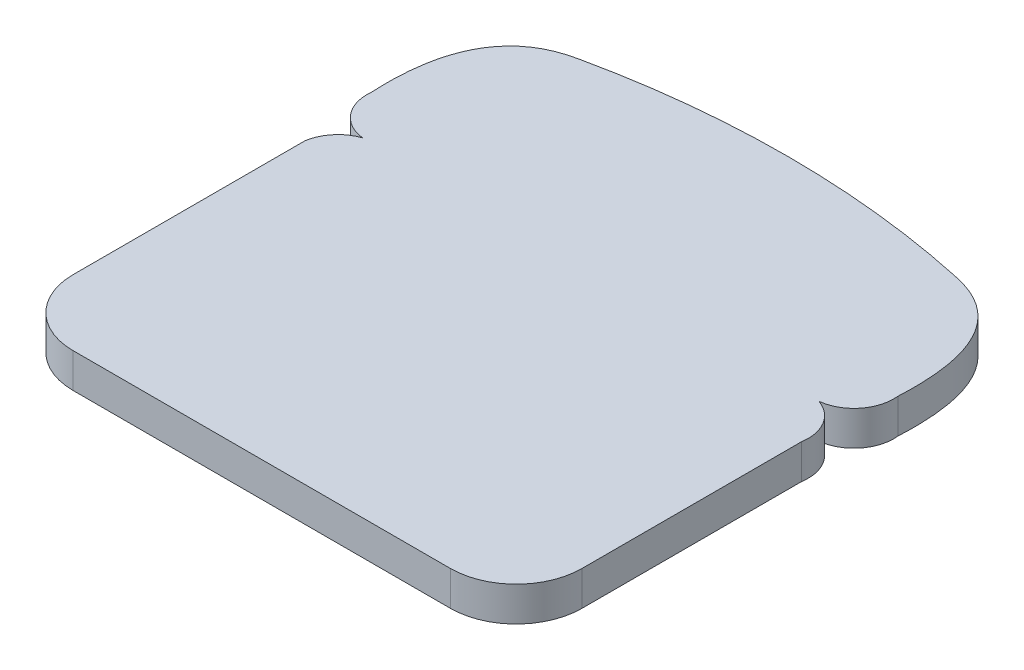
SolidWorks part; units mm, degrees
material "Teak"
ref_plane "Front Plane" through (0, 0, 0) normal (0, 0, 1) x (1, 0, 0)
ref_plane "Top Plane" through (0, 0, 0) normal (0, 1, 0) x (1, 0, 0)
ref_plane "Right Plane" through (0, 0, 0) normal (1, 0, 0) x (0, 0, -1)
sketch "Sketch2" plane through (0, 0, 0) normal (0, 1, 0) x (1, 0, 0)
  line L0 (-66.04, 22.225) -> (66.04, 22.225)
  line L1 (63.5, -66.675) -> (-63.5, -66.675)
  line L2 (63.5, -66.675) -> (63.5, 66.675)
  line L3 (63.5, 66.675) -> (-63.5, 66.675)
  line L4 (-63.5, -66.675) -> (-63.5, 66.675)
  line L5 (63.5, -66.675) -> (-63.5, 66.675) construction
  line L6 (63.5, 66.675) -> (-63.5, -66.675) construction
  line L7 (-73.66, 9.525) -> (-73.66, -53.975)
  line L8 (-54.61, -73.025) -> (54.61, -73.025)
  line L9 (73.66, -53.975) -> (73.66, 9.525)
  line L10 (-73.66, 9.525) -> (-73.66, 13.1711)
  line L11 (0, 79.1198) -> (-97.0113, 79.1198)
  arc A0 (-73.66, 9.525) -> (-66.04, 22.225) centre (-62.3051, 11.348) cw
  arc A1 (73.66, 9.525) -> (66.04, 22.225) centre (62.3051, 11.348) ccw
  arc A2 (-66.04, 22.225) -> (-76.2, 34.925) centre (-64.77, 33.655) cw
  arc A3 (66.04, 22.225) -> (76.2, 34.925) centre (64.77, 33.655) ccw
  arc A4 (-54.2615, 73.3341) -> (54.2615, 73.3341) centre (0, -178.2209) cw
  arc A5 (73.66, -53.975) -> (54.61, -73.025) centre (54.61, -53.975) cw
  arc A6 (-73.66, -53.975) -> (-54.61, -73.025) centre (-54.61, -53.975) ccw
  spline S0 degree 2 poles (-54.2615, 73.3341) (-78.0337, 68.7721) (-76.2, 34.925) knots 0 0 0 1 1 1
  spline S1 degree 2 poles (54.2615, 73.3341) (78.0337, 68.7721) (76.2, 34.925) knots 0 0 0 1 1 1
  point P0 (0, 0)
  dimension "D11" = 11.5003
  dimension "D12" = 11.5003
  dimension "D14" = 11.5003
  dimension "D15" = 11.5003
  dimension "D17" = 19.05
  dimension "D1" = 133.35
  dimension "D2" = 127
  dimension "D3" = 44.45
  dimension "D4" = 2.54
  dimension "D5" = 2.54
  dimension "D6" = 10.16
  dimension "D7" = 10.16
  dimension "D8" = 6.35
  dimension "D9" = 12.7
  dimension "D10" = 12.7
  dimension "D13" = 12.7
extrude "Boss-Extrude1" add sketch "Sketch2" along normal blind 10
